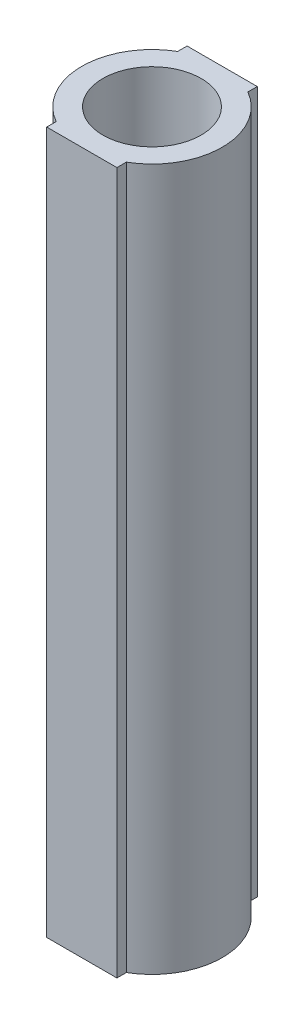
SolidWorks part; units mm, degrees
ref_plane "Front Plane" through (0, 0, 0) normal (0, 0, 1) x (1, 0, 0)
ref_plane "Top Plane" through (0, 0, 0) normal (0, 1, 0) x (1, 0, 0)
ref_plane "Right Plane" through (0, 0, 0) normal (1, 0, 0) x (0, 0, -1)
sketch "Sketch1" plane through (0, 0, 0) normal (0, 1, 0) x (1, 0, 0)
  circle A0 centre (0, 0) radius 7
  circle A1 centre (0, 0) radius 10
  dimension "D1" = 14
  dimension "D2" = 3
extrude "Boss-Extrude1" add sketch "Sketch1" along normal blind 100
sketch "Sketch2" plane through (0, 100, 0) normal (0, 1, 0) x (1, 0, 0)
  line L1 (-5, 10) -> (5, 10)
  line L2 (-5, 10) -> (-5, -10)
  line L3 (-5, -10) -> (5, -10)
  line L4 (5, 10) -> (5, -10)
  line L5 (-5, 10) -> (5, -10) construction
  line L6 (-5, -10) -> (5, 10) construction
  circle A0 centre (0, 0) radius 10
  point P0 (0, 0)
  circle M5 centre (0, 0) radius 10
  dimension "D1" = 20
  dimension "D2" = 10
extrude "Boss-Extrude2" add sketch "Sketch2" against normal blind 100 contours L1 L2 M5 | L4 L1 M5 | L2 L3 M5 | L4 L3 M5
